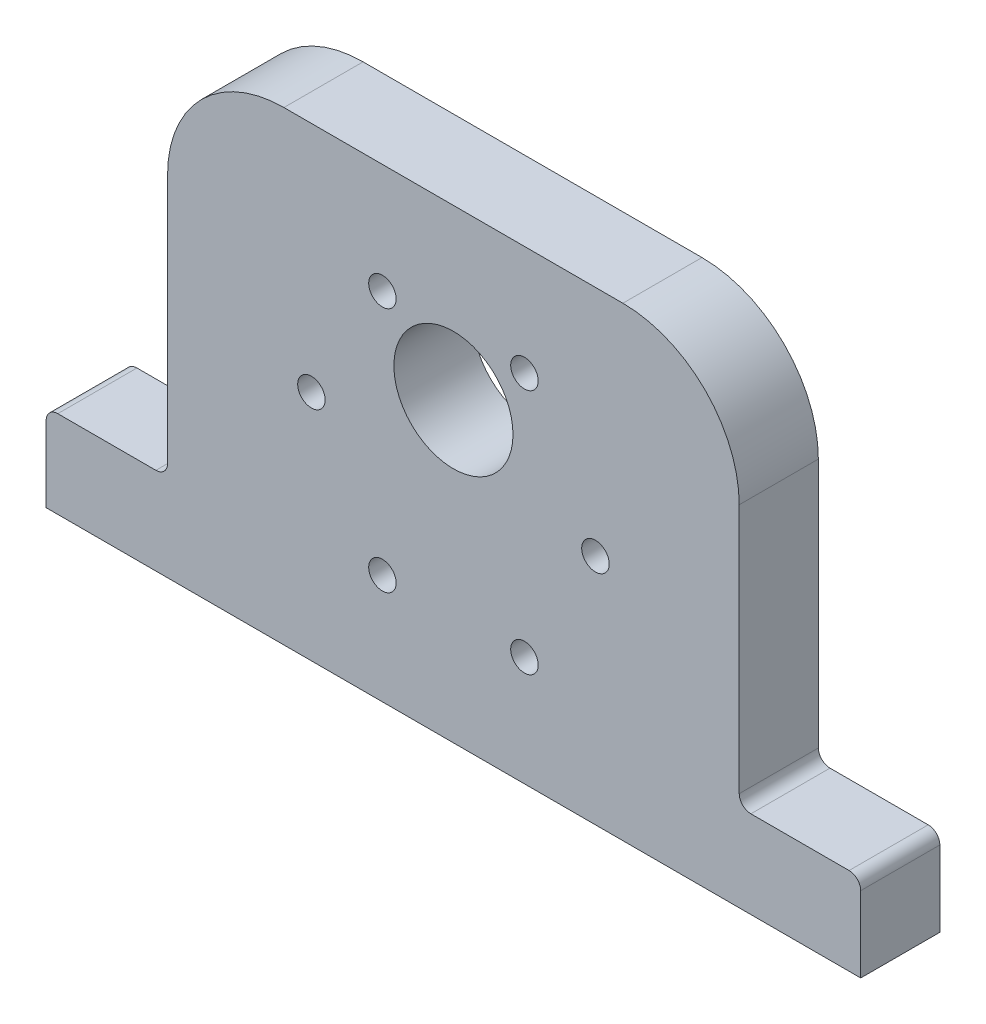
SolidWorks part; units mm, degrees
ref_plane "Front Plane" through (0, 0, 0) normal (0, 0, 1) x (1, 0, 0)
ref_plane "Top Plane" through (0, 0, 0) normal (0, 1, 0) x (1, 0, 0)
ref_plane "Right Plane" through (0, 0, 0) normal (1, 0, 0) x (0, 0, -1)
sketch "Sketch1" plane through (0, 0, 0) normal (0, 0, 1) x (1, 0, 0)
  line L0 (44.45, 50.8) -> (44.45, 0) construction
  line L1 (0, 0) -> (88.9, 0)
  line L2 (0, 0) -> (0, 9.525)
  line L3 (13.25, 50.8) -> (75.6412, 50.8)
  line L4 (88.9, 0) -> (88.9, 9.525)
  line L5 (0, 25.4) -> (88.9, 25.4) construction
  line L6 (44.45, 25.4) -> (76.4513, 80.8279) construction
  line L7 (44.45, 25.4) -> (81.7416, -39.1909) construction
  line L8 (0, 9.525) -> (13.25, 9.525)
  line L9 (13.25, 9.525) -> (13.25, 50.8)
  line L10 (75.6412, 50.8) -> (75.6412, 9.525)
  line L11 (75.6412, 9.525) -> (88.9, 9.525)
  circle A0 centre (44.45, 32.4) radius 6.5
  circle A1 centre (44.45, 25.4) radius 18.5 construction
  circle A2 centre (28.95, 25.4) radius 1.5
  circle A3 centre (59.95, 25.4) radius 1.5
  circle A4 centre (52.2, 11.9766) radius 1.5
  circle A5 centre (36.7, 11.9766) radius 1.5
  circle A6 centre (36.7, 38.8234) radius 1.5
  circle A7 centre (52.2, 38.8234) radius 1.5
  circle A8 centre (44.45, 25.4) radius 15.5 construction
  point P1 (0, 0)
  dimension "D3" = 13
  dimension "D4" = 37
  dimension "D7" = 3
  dimension "D10" = 31
  dimension "D1" = 88.9
  dimension "D2" = 50.8
  dimension "D5" = 7
  dimension "D6" = 25.4
  dimension "D8" = 60
  dimension "D9" = 60
  dimension "D11" = 31.2
  dimension "D12" = 9.525
  dimension "D13" = 31.1912
  dimension "D14" = 9.525
extrude "Boss-Extrude1" add sketch "Sketch1" along normal blind 8.636
fillet "Fillet1" radius 12.7 2 edges at (75.6412, 50.8, 4.318) (13.25, 50.8, 4.318)
fillet "Fillet2" radius 1.27 4 edges at (75.6412, 9.525, 4.318) (88.9, 9.525, 4.318) (13.25, 9.525, 4.318) (0, 9.525, 4.318)
